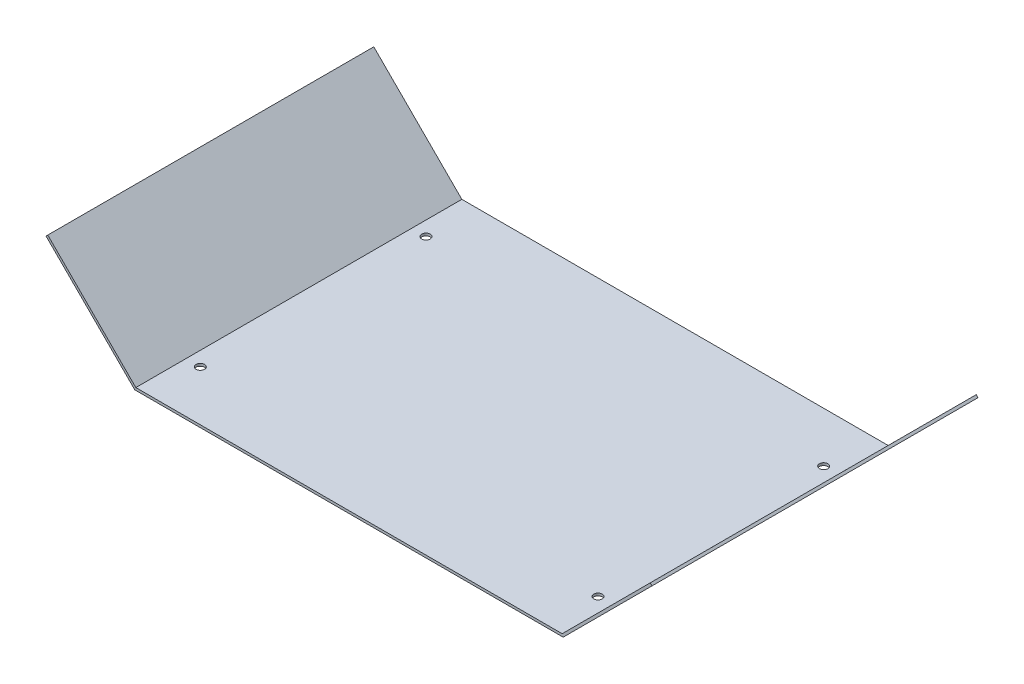
SolidWorks part; units mm, degrees
ref_plane "Plan de face" through (0, 0, 0) normal (0, 0, 1) x (1, 0, 0)
ref_plane "Plan de dessus" through (0, 0, 0) normal (0, 1, 0) x (1, 0, 0)
ref_plane "Plan de droite" through (0, 0, 0) normal (1, 0, 0) x (0, 0, -1)
sketch "Esquisse2" plane through (0, 0, 0) normal (0, 0, 1) x (1, 0, 0)
  line L0 (-59.1707, 35.114) -> (-24.0577, 0)
  line L1 (-24.0577, 0) -> (145.9423, 0)
  line L2 (145.9423, 0) -> (181.0563, 35.113)
  dimension "D1" = 170
  dimension "D2" = 49.658
  dimension "D3" = 49.658
  dimension "D4" = 35.114
extrude "Extru.-Mince1" add sketch "Esquisse2" along normal blind 130 thin
sketch "Esquisse12" plane through (0, 0, 0) normal (0, 1, 0) x (1, 0, 0)
  line L0 (-24.0577, -130) -> (-24.0577, 0) construction
  line L1 (145.9423, -130) -> (145.9423, 0) construction
  line L2 (-24.0577, 0) -> (145.9423, 0) construction
  line L3 (-24.0577, -130) -> (145.9423, -130) construction
  line L4 (-24.0577, 0) -> (145.9423, 0) construction
  point P0 (-18.3577, -20)
  point P1 (-18.3577, -110)
  point P2 (140.2423, -110)
  point P3 (140.2423, -20)
  dimension "D1" = 5.7
  dimension "D2" = 5.7
  dimension "D3" = 5.7
  dimension "D4" = 5.7
  dimension "D5" = 20
  dimension "D6" = 20
  dimension "D7" = 20
  dimension "D8" = 20
hole_wizard "Dégagement M32" positions "Esquisse14" profile "Esquisse13" hole size "M3" standard "ISO" end condition through all
sketch "Esquisse14" plane through (0, 0, 0) normal (0, 1, 0) x (-1, 0, 0)
  point P1 (18.3577, 20)
  point P4 (-140.2423, 20)
  point P7 (-140.2423, 110)
  point P10 (18.3577, 110)
sketch "Esquisse13" plane through (-18.3577, 0, 20) normal (1, 0, 0) x (0, 0, 1)
  line L0 (0, 0) -> (0, 1)
  line L1 (0, 1) -> (1.7, 1)
  line L2 (1.7, 1) -> (1.7, 0)
  line L5 (1.7, 0) -> (0, 0)
  line L11 (0, -6.35) -> (0, 107.95) construction
  dimension "Diamètre du perçage jusqu'au prochain" = 3.4
  dimension "Profondeur du perçage jusqu'au prochain" = 1
